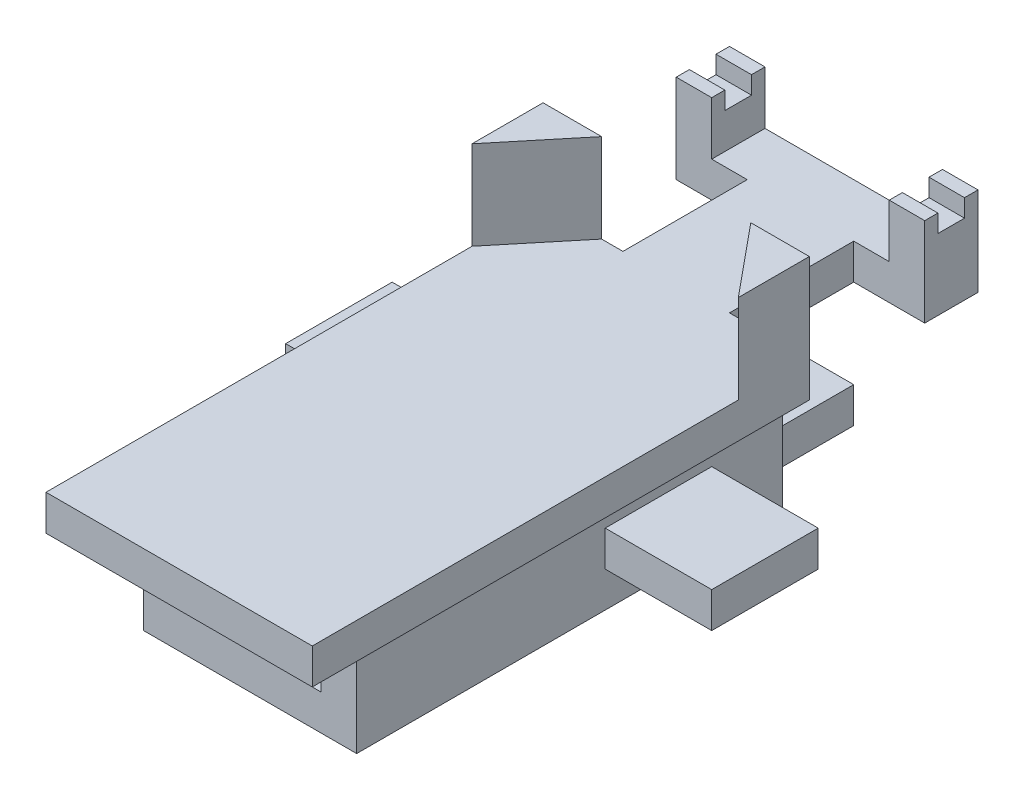
SolidWorks part; units mm, degrees
ref_plane "Front Plane" through (0, 0, 0) normal (0, 0, 1) x (1, 0, 0)
ref_plane "Top Plane" through (0, 0, 0) normal (0, 1, 0) x (1, 0, 0)
ref_plane "Right Plane" through (0, 0, 0) normal (1, 0, 0) x (0, 0, -1)
sketch "Sketch1" plane through (0, 0, 0) normal (0, 1, 0) x (1, 0, 0)
  line L1 (-3.75, -5) -> (3.75, -5)
  line L2 (-3.75, -5) -> (-3.75, 5)
  line L3 (-3.75, 5) -> (3.75, 5)
  line L4 (3.75, -5) -> (3.75, 5)
  line L5 (0, 5) -> (0, -5) construction
  line L6 (-3.75, 0) -> (3.75, 0) construction
  point P0 (0, 0)
  dimension "D1" = 10
  dimension "D2" = 7.5
extrude "Boss-Extrude1" add sketch "Sketch1" along normal blind 1
sketch "Sketch2" plane through (0, 1, 0) normal (0, 1, 0) x (1, 0, 0)
  line L0 (0, 5) -> (0, 3) construction
  line L1 (3.75, 5) -> (-3.75, 5) construction
  line L2 (-2.1, 5) -> (2.1, 5)
  line L3 (-2.1, 5) -> (-3.75, 3)
  line L4 (-3.75, 5) -> (-3.75, -5) construction
  line L5 (2.1, 5) -> (3.75, 3)
  line L6 (-3.75, 3) -> (-3.75, 5)
  line L7 (-3.75, 5) -> (-2.1, 5)
  line L8 (3.75, 3) -> (3.75, 5)
  line L9 (3.75, 5) -> (2.1, 5)
  point P8 (0, 5)
  line M2 (3.75, -5) -> (3.75, 5)
  line M3 (3.75, 5) -> (-3.75, 5)
  line M4 (-3.75, 5) -> (-3.75, -5)
  dimension "D1" = 2
extrude "Boss-Extrude2" add sketch "Sketch2" along normal blind 2.5 contours L3 M3 M4 | L5 M3 M2
ref_plane "Plane1" through (0, 3.5, 0) normal (0, 1, 0) x (1, 0, 0)
sketch "Sketch3" plane through (0, 3.5, 0) normal (0, 1, 0) x (1, 0, 0)
sketch "Sketch10" plane through (0, 0, 5) normal (0, 0, 1) x (1, 0, 0)
  line L1 (-3.75, 1) -> (3.75, 1)
  line L2 (-3.75, 1) -> (-3.75, 0)
  line L3 (-3.75, 0) -> (3.75, 0)
  line L4 (3.75, 1) -> (3.75, 0)
extrude "Boss-Extrude5" add sketch "Sketch10" along normal blind 2
sketch "Sketch56" plane through (0, 0, 7) normal (0, 0, 1) x (1, 0, 0)
  line L1 (-3.75, 1) -> (3.75, 1)
  line L2 (-3.75, 1) -> (-3.75, 0)
  line L3 (-3.75, 0) -> (3.75, 0)
  line L4 (3.75, 1) -> (3.75, 0)
extrude "Boss-Extrude17" add sketch "Sketch56" along normal blind 2
sketch "Sketch57" plane through (0, 0, -5) normal (0, 0, -1) x (-1, 0, 0)
  line L0 (0, 0) -> (0, 1) construction
  line L1 (-2.1, 1) -> (2.1, 1) construction
  line L3 (-1.5, 0) -> (1.5, 0)
  line L4 (-1.5, 0) -> (-1.5, 1)
  line L5 (-1.5, 1) -> (1.5, 1)
  line L6 (1.5, 0) -> (1.5, 1)
  line L7 (-1.5, 0) -> (1.5, 1) construction
  line L8 (-1.5, 1) -> (1.5, 0) construction
  point P5 (0, 0.5)
  dimension "D1" = 3
extrude "Boss-Extrude18" add sketch "Sketch57" along normal blind 5
sketch "Sketch58" plane through (1.5, 0, 0) normal (1, 0, 0) x (0, 0, -1)
  line L0 (10, 1) -> (5, 1) construction
  line L1 (10, 0) -> (8.5, 0)
  line L2 (10, 0) -> (10, 1)
  line L3 (10, 1) -> (8.5, 1)
  line L4 (8.5, 0) -> (8.5, 1)
  dimension "D1" = 1.5
extrude "Boss-Extrude19" add sketch "Sketch58" along normal blind 2
sketch "Sketch59" plane through (-1.5, 0, 0) normal (-1, 0, 0) x (0, 0, 1)
  line L0 (-10, 1) -> (-5, 1) construction
  line L1 (-10, 0) -> (-8.5, 0)
  line L2 (-10, 0) -> (-10, 1)
  line L3 (-10, 1) -> (-8.5, 1)
  line L4 (-8.5, 0) -> (-8.5, 1)
  dimension "D1" = 1.5
extrude "Boss-Extrude20" add sketch "Sketch59" along normal blind 2
sketch "Sketch60" plane through (0, 1, 0) normal (0, 1, 0) x (1, 0, 0)
  line L0 (3.5, 9.25) -> (2.5, 9.25) construction
  line L1 (3.5, 10) -> (3.5, 8.5) construction
  line L2 (3.5, 8.5) -> (1.5, 8.5) construction
  line L3 (2.5, 8.75) -> (2.5, 9.75)
  line L4 (0, 10) -> (0, 9.0116) construction
  line L5 (2.5, 8.5) -> (3.5, 8.5)
  line L6 (2.5, 8.5) -> (2.5, 10)
  line L7 (2.5, 10) -> (3.5, 10)
  line L8 (3.5, 8.5) -> (3.5, 10)
  line L9 (-3.5, 10) -> (3.5, 10) construction
  line L10 (2.5, 8.5) -> (3.5, 8.5)
  line L11 (2.5, 10) -> (3.5, 10)
  line L12 (-3.5, 9.25) -> (-2.5, 9.25) construction
  line L13 (-2.5, 10) -> (-3.5, 10)
  line L14 (-2.5, 8.5) -> (-3.5, 8.5)
  line L15 (-3.5, 8.5) -> (-3.5, 10)
  line L16 (-2.5, 10) -> (-3.5, 10)
  line L17 (-2.5, 8.5) -> (-2.5, 10)
  line L18 (-2.5, 8.5) -> (-3.5, 8.5)
  line L19 (-2.5, 8.75) -> (-2.5, 9.75)
  point P6 (2.5, 8.5)
  point P10 (2.5, 9.25)
  dimension "D1" = 1
extrude "Boss-Extrude23" add sketch "Sketch60" along normal blind 1.5 contours L8 L17 L6 L7 | L6 L4 L5 L3
sketch "Sketch61" plane through (0, 2.5, 0) normal (0, 1, 0) x (1, 0, 0)
  line L0 (2.5, 8.8704) -> (2.5, 9.6204)
  line L1 (-3.5, 10) -> (-3.5, 8.5) construction
  line L3 (-3.5, 8.8704) -> (-3.5, 9.6204)
  line L4 (-2.5, 8.5) -> (-2.5, 10) construction
  line L5 (-3.5, 8.8704) -> (-2.5, 8.8704)
  line L6 (-3.5, 8.8704) -> (-3.5, 9.6204)
  line L7 (-3.5, 9.6204) -> (-2.5, 9.6204)
  line L8 (-2.5, 8.8704) -> (-2.5, 9.6204)
  line L9 (0, 10) -> (0, 8.8704) construction
  line L10 (-2.5, 10) -> (2.5, 10) construction
  line L11 (3.5, 9.6204) -> (2.5, 9.6204)
  line L12 (3.5, 8.8704) -> (3.5, 9.6204)
  line L13 (3.5, 8.8704) -> (2.5, 8.8704)
  line L14 (3.5, 8.8704) -> (3.5, 9.6204)
  point P9 (-3.5, 9.2454)
  point P18 (3.5, 9.2454)
  point P19 (0, 0)
  line M3 (2.5, 10) -> (2.5, 8.5)
  line M5 (3.5, 8.5) -> (3.5, 10)
  dimension "D1" = 0.75
extrude "Cut-Extrude1" cut sketch "Sketch61" against normal blind 0.5 contours L5 L8 L7 L3 | L13 L11 M5 M3
sketch "Sketch62" plane through (0, 0, 0) normal (0, -1, 0) x (-1, 0, 0)
  line L0 (-1.5, 5) -> (1.5, 5)
  line L1 (0, 5) -> (0, -7) construction
  line L2 (3, -7) -> (-3, -7)
  line L3 (-3.75, 5) -> (-1.5, 5) construction
  line L4 (3, -7) -> (-3, -7)
  line L5 (3, -7) -> (3, 5)
  line L6 (3, 5) -> (-3, 5)
  line L7 (-3, -7) -> (-3, 5)
  point P10 (0, -7)
  line M5 (3.75, 5) -> (1.5, 5)
  line M13 (-1.5, 5) -> (-3.75, 5)
  dimension "D1" = 12
extrude "Boss-Extrude25" add sketch "Sketch62" along normal blind 3 contours L6 L1 L2 L5 M5 | L1 L0 L7 L4 M13
sketch "Sketch64" plane through (0, 0, 7) normal (0, 0, 1) x (1, 0, 0)
  line L0 (-2, 0) -> (2, 0)
  line L2 (-3.75, 0) -> (3.75, 0) construction
  line L4 (-2, 0) -> (2, 0)
  line L5 (-2, 0) -> (-2, -2)
  line L6 (-2, -2) -> (2, -2)
  line L7 (2, 0) -> (2, -2)
  point P7 (0, 0)
  line M2 (3, 0) -> (-3, 0)
  dimension "D1" = 2
extrude "Cut-Extrude2" cut sketch "Sketch64" against normal up to surface (12 mm away) contours L7 L5 L6 M2 up to face at (0.0375, 0.8281, -5)
sketch "Sketch65" plane through (0, 0, -5) normal (0, 0, -1) x (-1, 0, 0)
  line L0 (-3, -3) -> (3, -3) construction
  line L1 (-2, -2) -> (2, -2)
  line L2 (-2, -2) -> (-2, -3)
  line L3 (-2, -3) -> (2, -3)
  line L4 (2, -2) -> (2, -3)
  dimension "D1" = 4
extrude "Boss-Extrude26" add sketch "Sketch65" along normal blind 3
sketch "Sketch66" plane through (0, -3, 0) normal (0, -1, 0) x (-1, 0, 0)
  line L0 (0, -7) -> (0, -5) construction
  line L1 (0, -5) -> (0, 5) construction
  line L2 (3, -7) -> (-3, -7) construction
  circle A0 centre (0, -5) radius 1
  circle A1 centre (0, 5) radius 1
  dimension "D2" = 10
  dimension "D1" = 2
extrude "Cut-Extrude3" cut sketch "Sketch66" against normal up to surface (1 mm away) up to face at (0, -2, -2)
sketch "Sketch67" plane through (-3, 0, 0) normal (-1, 0, 0) x (0, 0, 1)
  line L0 (-5, 0) -> (-3, 0)
  line L1 (-5, 0) -> (9, 0) construction
  line L2 (-3, 0) -> (-3, -1)
  line L4 (-3, -1) -> (0, -1)
  line L5 (-3, -1) -> (-3, -2)
  line L6 (-3, -2) -> (0, -2)
  line L7 (0, -1) -> (0, -2)
  dimension "D1" = 2
  dimension "D2" = 1
  dimension "D3" = 1
  dimension "D4" = 3
extrude "Boss-Extrude27" add sketch "Sketch67" along normal blind 3 contours L7 L4 L5 L6
sketch "Sketch68" plane through (3, 0, 0) normal (1, 0, 0) x (0, 0, -1)
  line L0 (5, 0) -> (3, 0)
  line L1 (-9, 0) -> (5, 0) construction
  line L2 (3, 0) -> (3, -1)
  line L4 (3, -1) -> (0, -1)
  line L5 (3, -1) -> (3, -2)
  line L6 (3, -2) -> (0, -2)
  line L7 (0, -1) -> (0, -2)
  dimension "D1" = 2
  dimension "D2" = 1
  dimension "D3" = 3
  dimension "D4" = 1
extrude "Boss-Extrude28" add sketch "Sketch68" along normal blind 3 contours L4 L7 L6 L5
